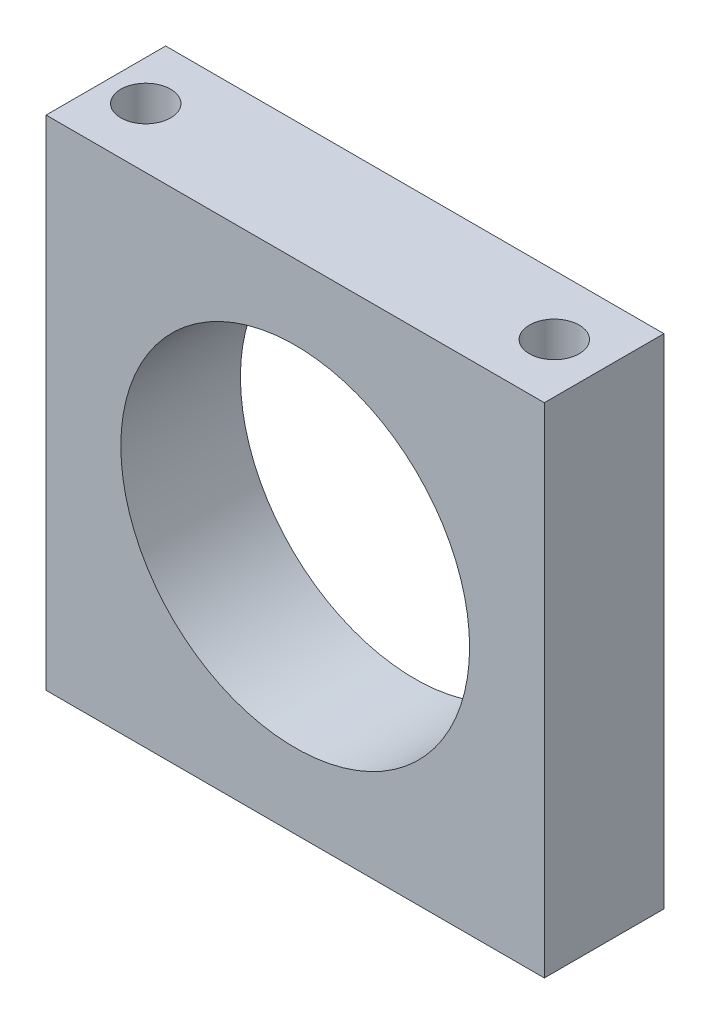
SolidWorks part; units mm, degrees
ref_plane "Piano frontale" through (0, 0, 0) normal (0, 0, 1) x (1, 0, 0)
ref_plane "Piano superiore" through (0, 0, 0) normal (0, 1, 0) x (1, 0, 0)
ref_plane "Piano destro" through (0, 0, 0) normal (1, 0, 0) x (0, 0, -1)
sketch "Schizzo1" plane through (0, 0, 0) normal (0, 0, 1) x (1, 0, 0)
  line L1 (-25, -25) -> (25, -25)
  line L2 (-25, -25) -> (-25, 25)
  line L3 (-25, 25) -> (25, 25)
  line L4 (25, -25) -> (25, 25)
  line L5 (-25, -25) -> (25, 25) construction
  line L6 (-25, 25) -> (25, -25) construction
  circle A0 centre (0, 0) radius 17.5
  point P0 (0, 0)
  dimension "D3" = 35
  dimension "D1" = 50
  dimension "D2" = 50
extrude "Estrusione-Estrusione1" add sketch "Schizzo1" along normal blind 12
sketch "Schizzo2" plane through (0, -25, 0) normal (0, -1, 0) x (-1, 0, 0)
  line L0 (25, -12) -> (25, 0) construction
  line L1 (-25, -12) -> (-25, 0) construction
  line L2 (25, 0) -> (-25, 0) construction
  circle A0 centre (21, -6) radius 2.5
  circle A1 centre (-20, -6) radius 2.5
  dimension "D3" = 5
  dimension "D4" = 5
  dimension "D1" = 4
  dimension "D2" = 5
  dimension "D5" = 6
  dimension "D6" = 6
extrude "Taglio-Estrusione1" cut sketch "Schizzo2" against normal blind 5
sketch "Schizzo3" plane through (0, 25, 0) normal (0, 1, 0) x (1, 0, 0)
  line L0 (25, -12) -> (25, 0) construction
  line L1 (-25, -12) -> (-25, 0) construction
  line L2 (25, 0) -> (-25, 0) construction
  circle A0 centre (20, -6) radius 2.5
  circle A1 centre (-21, -6) radius 2.5
  dimension "D1" = 5
  dimension "D2" = 5
  dimension "D3" = 5
  dimension "D4" = 4
  dimension "D5" = 6
  dimension "D6" = 6
extrude "Taglio-Estrusione2" cut sketch "Schizzo3" against normal blind 5
